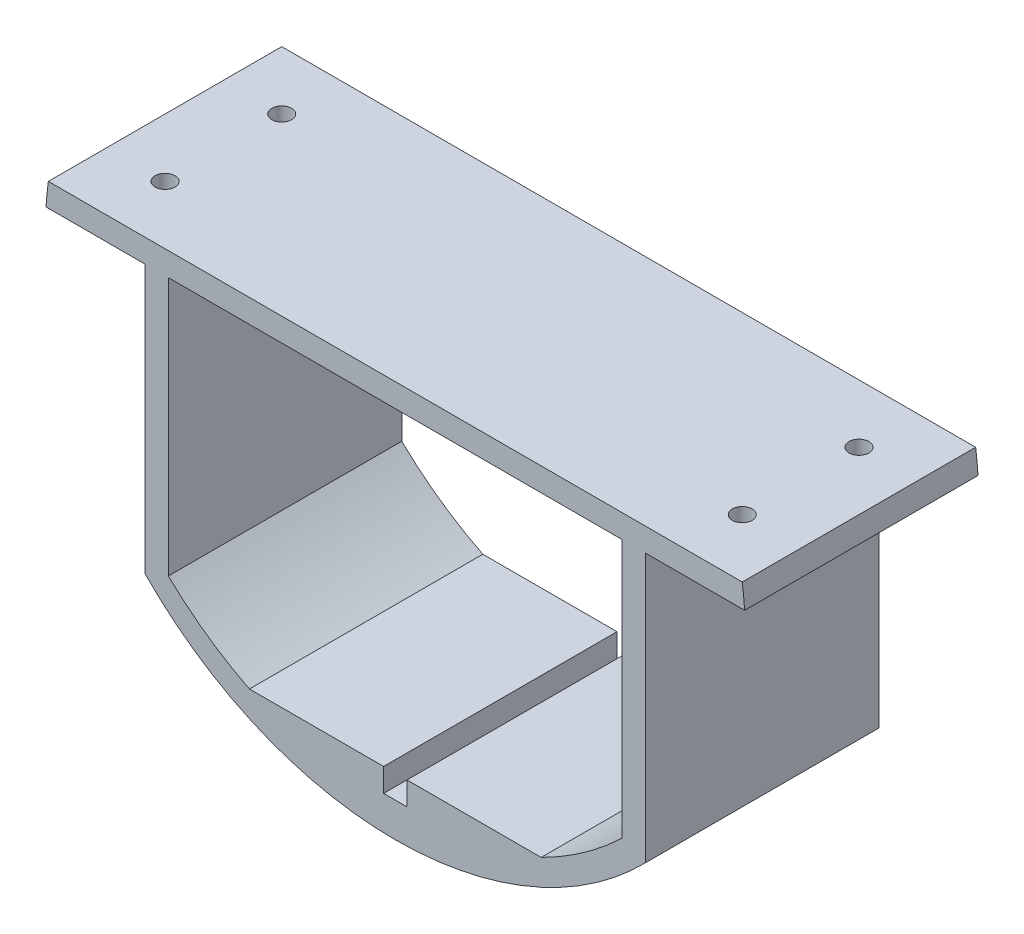
SolidWorks part; units mm, degrees
ref_plane "Front Plane" through (0, 0, 0) normal (0, 0, 1) x (1, 0, 0)
ref_plane "Top Plane" through (0, 0, 0) normal (0, 1, 0) x (1, 0, 0)
ref_plane "Right Plane" through (0, 0, 0) normal (1, 0, 0) x (0, 0, -1)
sketch "Sketch2" plane through (0, 0, 0) normal (0, 0, 1) x (1, 0, 0)
  circle A0 centre (0, 0) radius 76.2
extrude "Boss-Extrude1" add sketch "Sketch2" along normal blind 50.8
sketch "Sketch4" plane through (0, 0, 50.8) normal (0, 0, 1) x (1, 0, 0)
  line L0 (-75.5196, 10.16) -> (75.5196, 10.16)
  circle A0 centre (0, 0) radius 76.2 construction
  arc A1 (-75.5196, 10.16) -> (75.5196, 10.16) centre (0, 0) cw
  dimension "D1" = 10.16
extrude "Cut-Extrude1" cut sketch "Sketch4" against normal blind 76.2
sketch "Sketch5" plane through (0, 0, 50.8) normal (0, 0, 1) x (1, 0, 0)
  line L0 (-70.9383, 5.08) -> (70.9383, 5.08)
  line L1 (-31.75, -63.6395) -> (31.75, -63.6395)
  line L2 (-75.5196, 10.16) -> (75.5196, 10.16) construction
  line L3 (54.4769, 5.08) -> (54.4769, -45.72)
  line L4 (-54.4769, 5.08) -> (-54.4769, -45.72)
  line L5 (49.3969, 5.08) -> (49.3969, -51.1664)
  line L6 (-49.3969, 5.08) -> (-49.3969, -51.1664)
  arc A0 (-70.9383, 5.08) -> (70.9383, 5.08) centre (0, 0) ccw
  arc A1 (-75.5196, 10.16) -> (75.5196, 10.16) centre (0, 0) ccw construction
  point P10 (0, 10.16)
  dimension "D1" = 0
  dimension "D3" = 5.08
  dimension "D2" = 5.08
  dimension "D4" = 63.5
  dimension "D5" = 50.8
  dimension "D6" = 50.8
  dimension "D7" = 5.08
  dimension "D8" = 5.08
extrude "Cut-Extrude2" cut sketch "Sketch5" against normal blind 76.2 contours L0 A0 L1
sketch "Sketch8" plane through (0, 0, 50.8) normal (0, 0, 1) x (1, 0, 0)
  line L0 (-31.75, -63.6395) -> (31.75, -63.6395) construction
  line L1 (-2.54, -63.6395) -> (2.54, -63.6395)
  line L2 (-2.54, -63.6395) -> (-2.54, -68.7195)
  line L3 (-2.54, -68.7195) -> (2.54, -68.7195)
  line L4 (2.54, -63.6395) -> (2.54, -68.7195)
  dimension "D1" = 5.08
  dimension "D2" = 5.08
  dimension "D3" = 29.21
extrude "Cut-Extrude4" cut sketch "Sketch8" against normal blind 50.8
sketch "Sketch9" plane through (0, 0, 50.8) normal (0, 0, 1) x (1, 0, 0)
  line L0 (54.4769, 5.08) -> (76.0305, 5.08)
  line L1 (54.4769, 5.08) -> (54.4769, -53.2795)
  line L2 (49.3969, 5.08) -> (49.3969, -51.1664) construction
  line L3 (-54.4769, 5.08) -> (-54.4769, -53.2795)
  line L4 (-49.3969, 5.08) -> (-49.3969, -51.1664) construction
  line L5 (-54.4769, 5.08) -> (-76.0305, 5.08)
  arc A0 (-75.5196, 10.16) -> (75.5196, 10.16) centre (0, 0) ccw construction
  arc A1 (54.4769, -53.2795) -> (76.0305, 5.08) centre (0, 0) ccw
  arc A2 (-76.0305, 5.08) -> (-54.4769, -53.2795) centre (0, 0) ccw
  dimension "D1" = 5.08
  dimension "D2" = 5.08
extrude "Cut-Extrude5" cut sketch "Sketch9" against normal through all
sketch "Sketch10" plane through (0, 10.16, 0) normal (0, 1, 0) x (1, 0, 0)
  line L0 (-75.5196, -50.8) -> (75.5196, -50.8) construction
  line L2 (-75.5196, 0) -> (-75.5196, -50.8) construction
  line L4 (75.5196, 0) -> (75.5196, -50.8) construction
  line L5 (-75.5196, 0) -> (75.5196, 0) construction
  circle A4 centre (-62.8196, -12.7) radius 2.159
  circle A5 centre (-62.8196, -38.1) radius 2.159
  circle A6 centre (62.8196, -12.7) radius 2.159
  circle A7 centre (62.8196, -38.1) radius 2.159
  dimension "D1" = 4.318
  dimension "D2" = 12.7
  dimension "D3" = 12.7
  dimension "D4" = 12.7
  dimension "D5" = 12.7
  dimension "D6" = 12.7
  dimension "D7" = 12.7
  dimension "D8" = 12.7
  dimension "D9" = 12.7
extrude "Cut-Extrude6" cut sketch "Sketch10" against normal blind 25.4
